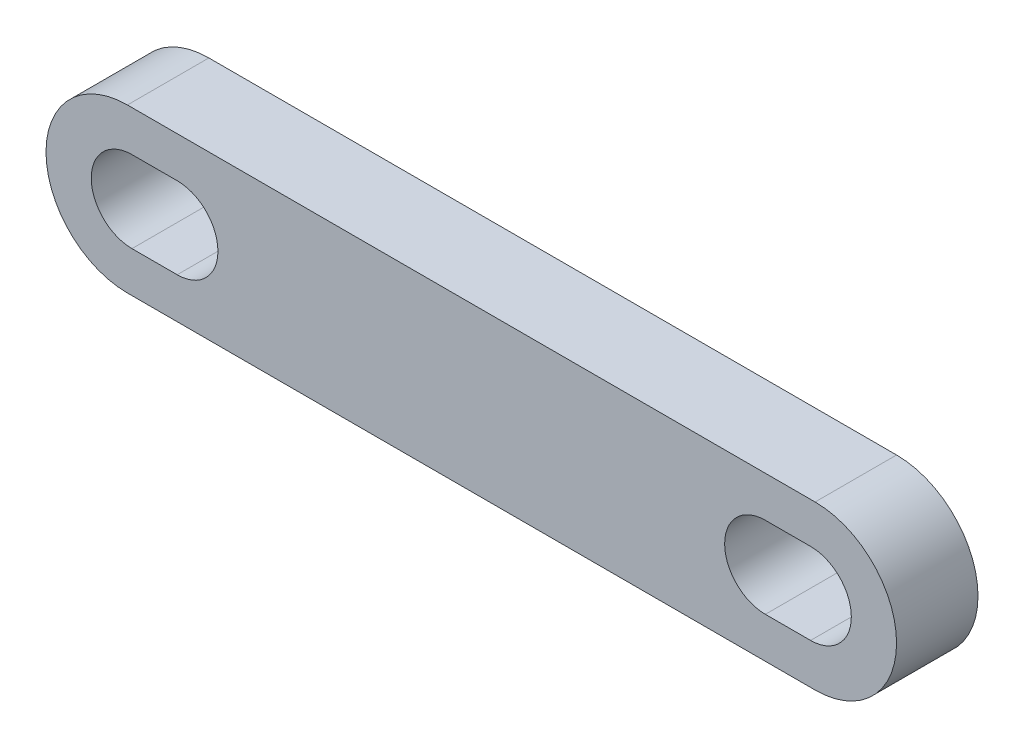
SolidWorks part; units mm, degrees
material "acero"
ref_plane "Alzado" through (0, 0, 0) normal (0, 0, 1) x (1, 0, 0)
ref_plane "Planta" through (0, 0, 0) normal (0, 1, 0) x (1, 0, 0)
ref_plane "Vista lateral" through (0, 0, 0) normal (1, 0, 0) x (0, 0, -1)
sketch "Croquis1" plane through (0, 0, 0) normal (0, 0, 1) x (1, 0, 0)
  line L2 (19, 4.5) -> (-19, 4.5)
  line L3 (-19, -4.5) -> (19, -4.5)
  line L4 (19, 4.5) -> (-19, 4.5)
  line L5 (-19, -4.5) -> (19, -4.5)
  line L10 (18.75, 2.25) -> (16.25, 2.25)
  line L11 (16.25, -2.25) -> (18.75, -2.25)
  line L12 (18.75, 2.25) -> (16.25, 2.25)
  line L13 (16.25, -2.25) -> (18.75, -2.25)
  line L14 (-16.25, 2.25) -> (-18.75, 2.25)
  line L15 (-18.75, -2.25) -> (-16.25, -2.25)
  line L16 (-16.25, 2.25) -> (-18.75, 2.25)
  line L17 (-18.75, -2.25) -> (-16.25, -2.25)
  arc A2 (-19, 4.5) -> (-19, -4.5) centre (-19, 0) ccw
  arc A3 (19, -4.5) -> (19, 4.5) centre (19, 0) ccw
  arc A4 (-19, 4.5) -> (-19, -4.5) centre (-19, 0) ccw
  arc A5 (19, -4.5) -> (19, 4.5) centre (19, 0) ccw
  arc A10 (16.25, 2.25) -> (16.25, -2.25) centre (16.25, 0) ccw
  arc A11 (18.75, -2.25) -> (18.75, 2.25) centre (18.75, 0) ccw
  arc A12 (16.25, 2.25) -> (16.25, -2.25) centre (16.25, 0) ccw
  arc A13 (18.75, -2.25) -> (18.75, 2.25) centre (18.75, 0) ccw
  arc A14 (-18.75, 2.25) -> (-18.75, -2.25) centre (-18.75, 0) ccw
  arc A15 (-16.25, -2.25) -> (-16.25, 2.25) centre (-16.25, 0) ccw
  arc A16 (-18.75, 2.25) -> (-18.75, -2.25) centre (-18.75, 0) ccw
  arc A17 (-16.25, -2.25) -> (-16.25, 2.25) centre (-16.25, 0) ccw
  dimension "D1" = 0
  dimension "D2" = 0
  dimension "D3" = 0
extrude "Saliente-Extruir2" add sketch "Croquis1" along normal up to surface (4.5 mm away)
